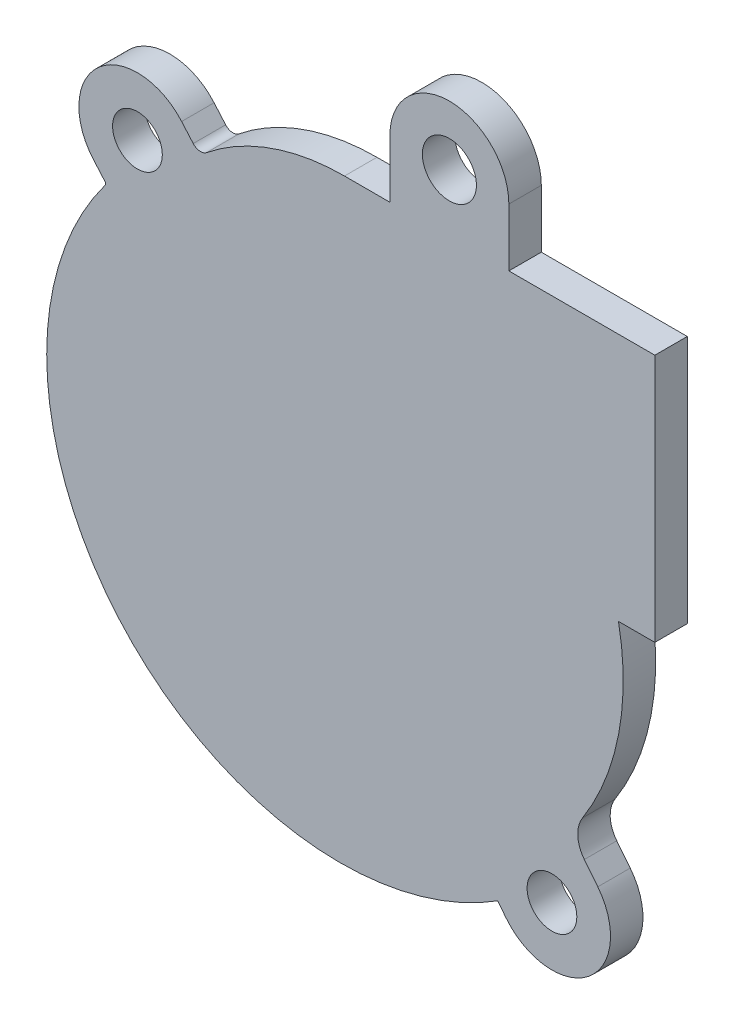
SolidWorks part; units mm, degrees
ref_plane "Front Plane" through (0, 0, 0) normal (0, 0, 1) x (1, 0, 0)
ref_plane "Top Plane" through (0, 0, 0) normal (0, 1, 0) x (1, 0, 0)
ref_plane "Right Plane" through (0, 0, 0) normal (1, 0, 0) x (0, 0, -1)
sketch "Sketch1" plane through (0, 0, 0) normal (0, 0, 1) x (1, 0, 0)
  line L34 (-11.5, 21) -> (2, 21)
  line L35 (-26.7, 21) -> (0, 21)
  line L36 (-26.7, 21) -> (-22.5, 21)
  line L38 (-11.5, 21) -> (-11.5, 26.3539)
  line L39 (2, -2) -> (2, 19)
  line L40 (-1.3601, -2) -> (2, -2)
  line L41 (-3.2772, -24.2141) -> (-4.5222, -22.6489)
  line L42 (-40.6906, 16.6073) -> (-41.76, 17.8376)
  line L43 (-49.9335, 10.7324) -> (-48.8641, 9.5022)
  line L44 (-12.5385, -29.9682) -> (-11.7528, -30.9559)
  line L45 (2, -2) -> (2, 21)
  line L46 (-1.3601, -2) -> (2, -2)
  line L47 (-3.2772, -24.2141) -> (-4.5222, -22.6489)
  line L48 (-40.6906, 16.6073) -> (-41.76, 17.8376)
  line L49 (-49.9335, 10.7324) -> (-48.8641, 9.5022)
  line L50 (-12.5385, -29.9682) -> (-11.7528, -30.9559)
  line L52 (-22.5, 21) -> (-22.5, 26.3539)
  circle A0 centre (-45.8468, 14.285) radius 2.3 construction
  circle A1 centre (-7.515, -27.585) radius 2.3 construction
  circle A2 centre (-45.8468, 14.285) radius 2.3
  circle A3 centre (-7.515, -27.585) radius 2.3
  arc A46 (-22.5, 26.3539) -> (-11.5, 26.3539) centre (-17, 26.3539) cw
  circle A47 centre (-17, 26.3539) radius 2.5
  arc A58 (-4.6886, -19.3986) -> (-1.3601, -2) centre (-24.7672, -6.5396) ccw
  arc A59 (-4.6886, -19.3986) -> (-4.5222, -22.6489) centre (-2.3329, -20.9074) ccw
  arc A60 (-26.7, 21) -> (-39.4554, 16.498) centre (-26.7, 0.6794) ccw
  arc A61 (-40.6906, 16.6073) -> (-39.4554, 16.498) centre (-40.0163, 17.1935) ccw
  arc A62 (-41.76, 17.8376) -> (-49.9335, 10.7324) centre (-45.8468, 14.285) ccw
  arc A63 (-48.8519, 9.175) -> (-48.8641, 9.5022) centre (-49.061, 9.331) ccw
  arc A64 (-48.8519, 9.175) -> (-29.9214, -34.0522) centre (-27.093, -7.0549) ccw
  arc A65 (-29.9214, -34.0522) -> (-24.2646, -34.0522) centre (-27.093, -7.0549) ccw
  arc A66 (-24.2646, -34.0522) -> (-12.5385, -29.9682) centre (-27.093, -7.0549) ccw
  arc A67 (-11.7528, -30.9559) -> (-3.2772, -24.2141) centre (-7.515, -27.585) ccw
  arc A68 (-4.6886, -19.3986) -> (-1.3601, -2) centre (-24.7672, -6.5396) ccw
  arc A69 (-4.6886, -19.3986) -> (-4.5222, -22.6489) centre (-2.3329, -20.9074) ccw
  arc A70 (-26.7, 21) -> (-39.4554, 16.498) centre (-26.7, 0.6794) ccw
  arc A71 (-40.6906, 16.6073) -> (-39.4554, 16.498) centre (-40.0163, 17.1935) ccw
  arc A72 (-41.76, 17.8376) -> (-49.9335, 10.7324) centre (-45.8468, 14.285) ccw
  arc A73 (-48.8519, 9.175) -> (-48.8641, 9.5022) centre (-49.061, 9.331) ccw
  arc A74 (-48.8519, 9.175) -> (-29.9214, -34.0522) centre (-27.093, -7.0549) ccw
  arc A75 (-29.9214, -34.0522) -> (-24.2646, -34.0522) centre (-27.093, -7.0549) ccw
  arc A76 (-24.2646, -34.0522) -> (-12.5385, -29.9682) centre (-27.093, -7.0549) ccw
  arc A77 (-11.7528, -30.9559) -> (-3.2772, -24.2141) centre (-7.515, -27.585) ccw
  dimension "D3" = 5.5
  dimension "D4" = 5
  dimension "D5" = 13.5
  dimension "D6" = 5.3539
  dimension "D1" = 2
  dimension "D2" = 2
extrude "Boss-Extrude1" add sketch "Sketch1" along normal blind 3
